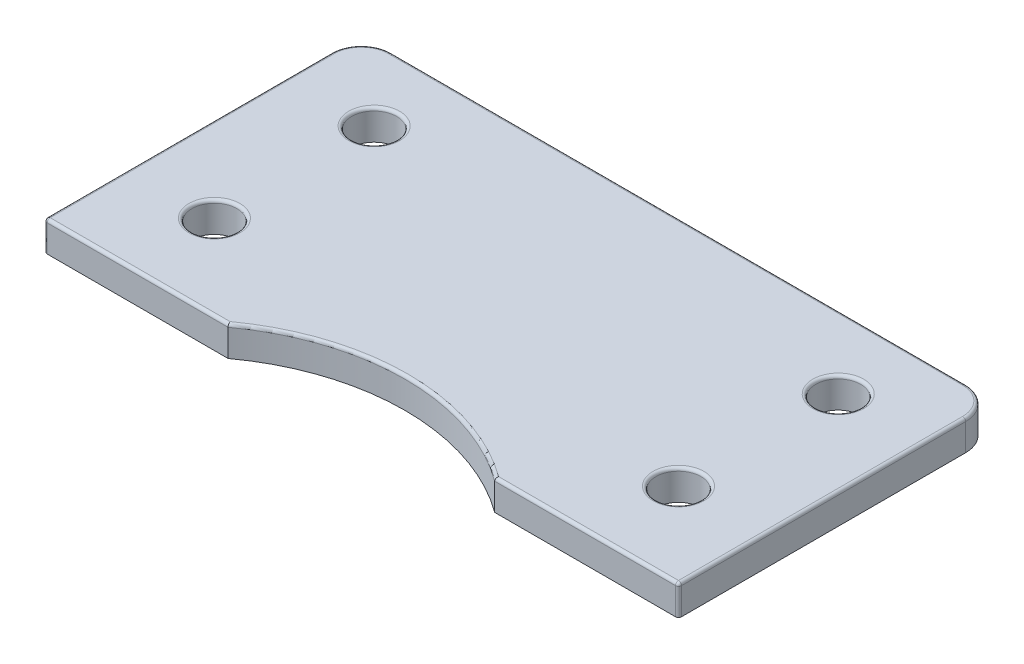
SolidWorks part; units mm, degrees
ref_plane "Front Plane" through (0, 0, 0) normal (0, 0, 1) x (1, 0, 0)
ref_plane "Top Plane" through (0, 0, 0) normal (0, 1, 0) x (1, 0, 0)
ref_plane "Right Plane" through (0, 0, 0) normal (1, 0, 0) x (0, 0, -1)
sketch "Sketch1" plane through (0, 0, 0) normal (0, 1, 0) x (1, 0, 0)
  line L0 (-15.4497, -15.5) -> (-15.4497, -21.15) construction
  line L1 (-15.4497, -15.5) -> (-15.4497, -10) construction
  line L2 (-21.15, -21.15) -> (-8.8917, -21.15)
  line L3 (21.15, -10) -> (-21.15, -10) construction
  line L4 (21.15, -21.15) -> (21.15, 0)
  line L5 (21.15, 0) -> (-21.15, 0)
  line L6 (15.5, -15.5) -> (21.15, -15.5) construction
  line L7 (0, -21.15) -> (0, -18.35) construction
  line L8 (0, -21.15) -> (8.8917, -21.15) construction
  line L9 (8.8917, -21.15) -> (21.15, -21.15)
  line L10 (-21.15, 0) -> (-21.15, -21.15)
  arc A0 (8.8917, -21.15) -> (-8.8917, -21.15) centre (0, -33.3221) ccw
  circle A1 centre (15.5, -4.8479) radius 1.5
  circle A2 centre (-15.4497, -15.5) radius 1.5
  circle A3 centre (15.5, -15.5) radius 1.5
  circle A4 centre (-15.4497, -4.8479) radius 1.5
extrude "Boss-Extrude1" add sketch "Sketch1" along normal blind 2
fillet "Fillet1" radius 2 2 edges at (-21.15, 1, 0) (21.15, 1, 0)
fillet "Fillet2" radius 0.2 14 edges at (-15.4497, 2, 6.3479) (15.5, 2, 17) (20.5642, 2, 0.5858) (21.15, 2, 11.575) (15.0209, 2, 21.15) (0, 2, 18.2482) (-15.0209, 2, 21.15) (-21.15, 2, 11.575) (-20.5642, 2, 0.5858) (0, 2, 0) (-15.4497, 2, 17) (15.5, 2, 6.3479) (-21.15, 1, 21.15) (21.15, 1, 21.15)
